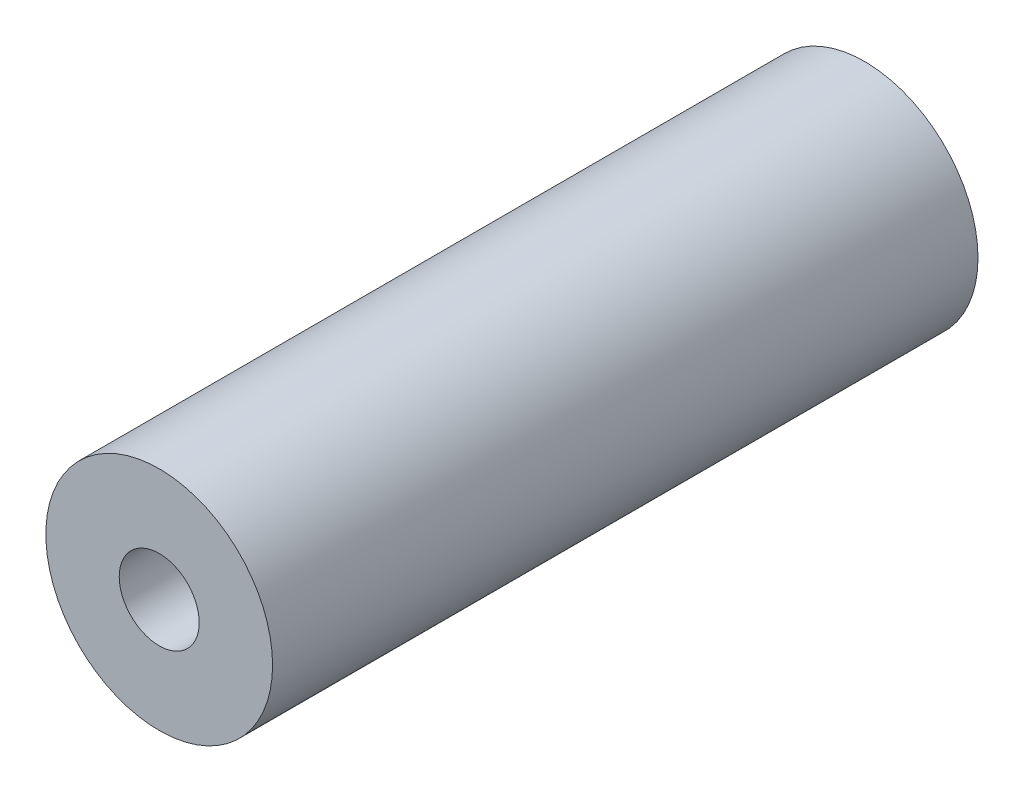
SolidWorks part; units mm, degrees
material "Borracha de silicone"
ref_plane "Plano frontal" through (0, 0, 0) normal (0, 0, 1) x (1, 0, 0)
ref_plane "Plano superior" through (0, 0, 0) normal (0, 1, 0) x (1, 0, 0)
ref_plane "Plano direito" through (0, 0, 0) normal (1, 0, 0) x (0, 0, -1)
sketch "Esboço1" plane through (0, 0, 0) normal (0, 0, 1) x (1, 0, 0)
  circle A0 centre (0, 0) radius 9
  dimension "D1" = 18
extrude "Ressalto-extrusão1" add sketch "Esboço1" along normal blind 56
sketch "Esboço2" plane through (0, 0, 0) normal (0, 0, -1) x (-1, 0, 0)
  circle A0 centre (0, 0) radius 5.615
  dimension "D1" = 11.23
extrude "Corte-extrusão1" cut sketch "Esboço2" against normal blind 7.54
sketch "Esboço3" plane through (0, 0, 7.54) normal (0, 0, -1) x (-1, 0, 0)
  circle A0 centre (0, 0) radius 3.175
  dimension "D1" = 6.35
extrude "Corte-extrusão2" cut sketch "Esboço3" against normal through all
